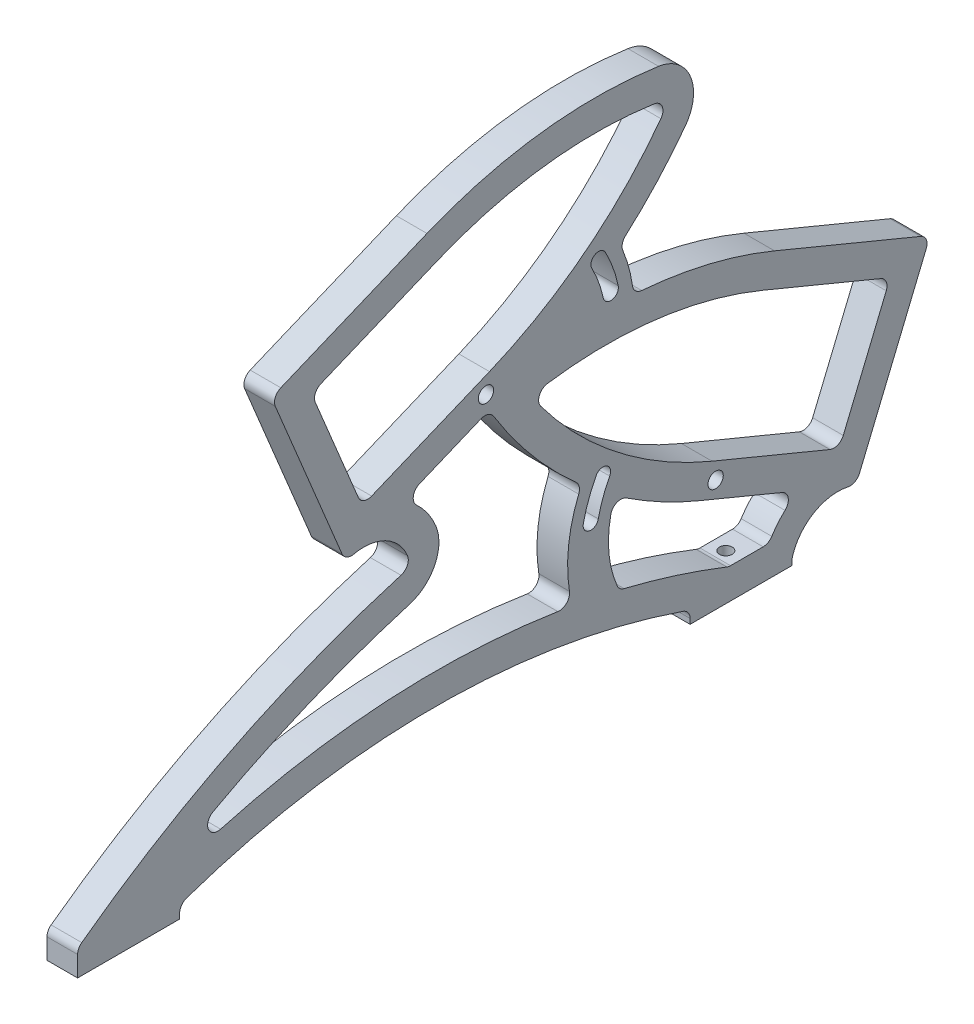
SolidWorks part; units mm, degrees
material "1060 Alloy"
ref_plane "Front Plane" through (0, 0, 0) normal (0, 0, 1) x (1, 0, 0)
ref_plane "Top Plane" through (0, 0, 0) normal (0, 1, 0) x (1, 0, 0)
ref_plane "Right Plane" through (0, 0, 0) normal (1, 0, 0) x (0, 0, -1)
sketch "Sketch1" plane through (0, 0, 0) normal (1, 0, 0) x (0, 0, -1)
  line L0 (0, 0) -> (0, 5)
  line L1 (38.8897, 79.8553) -> (54.5797, 41.9762) construction
  line L2 (38.8897, 79.8553) -> (112.8001, 110.47) construction
  line L3 (54.5797, 41.9762) -> (128.4901, 72.5909) construction
  line L4 (41.8855, 77.849) -> (54.1314, 48.2849) construction
  line L5 (112.8001, 110.47) -> (128.4901, 72.5909) construction
  line L6 (20, 1) -> (20, 0)
  line L7 (0, 0) -> (20, 0)
  line L8 (54.1314, 48.2849) -> (81.8478, 59.7654) construction
  line L9 (69.6019, 89.3295) -> (41.8855, 77.849) construction
  line L10 (80, 59) -> (104.4537, 64.1978) construction
  line L11 (102.0737, 70.7368) -> (80, 59) construction
  line L12 (100.5463, 27.1978) -> (125, 22) construction
  line L13 (125, 22) -> (102.9263, 33.7368) construction
  line L14 (166.1103, 42.8553) -> (150.4203, 4.9762) construction
  line L15 (166.1103, 42.8553) -> (92.1999, 73.47) construction
  line L16 (150.4203, 4.9762) -> (76.5099, 35.5909) construction
  line L17 (92.1999, 73.47) -> (76.5099, 35.5909) construction
  line L18 (150.8686, 11.2849) -> (163.1145, 40.849) construction
  line L19 (163.1145, 40.849) -> (135.3981, 52.3295) construction
  line L20 (123.1522, 22.7654) -> (150.8686, 11.2849) construction
  line L21 (156.9916, 26.0669) -> (84.929, 55.9162) construction
  line L22 (48.0084, 63.0669) -> (120.071, 92.9162) construction
  line L23 (152.4922, 7.3652) -> (167.0342, 42.4726)
  line L24 (167.0342, 42.4726) -> (136.5462, 55.1012)
  line L25 (68.4538, 92.1012) -> (37.9658, 79.4726)
  line L26 (37.9658, 79.4726) -> (52.5078, 44.3652)
  line L27 (63.7245, 49.0113) -> (80.6343, 56.0156)
  line L28 (140, 0) -> (140, 1)
  line L29 (152.4922, 7.3652) -> (143.6238, 11.0386) construction
  line L30 (80.6997, 62.537) -> (55.755, 52.2046)
  line L31 (55.755, 52.2046) -> (45.8052, 76.2254)
  line L32 (45.8052, 76.2254) -> (70.7499, 86.5579)
  line L33 (124.3003, 25.537) -> (149.245, 15.2046)
  line L34 (149.245, 15.2046) -> (159.1948, 39.2254)
  line L35 (159.1948, 39.2254) -> (134.2501, 49.5579)
  line L36 (56.0604, 35.7884) -> (62.7895, 38.5756) construction
  line L37 (52.5078, 44.3652) -> (58.8317, 46.9846) construction
  line L38 (122.0042, 19.9937) -> (141.2755, 12.0113)
  line L39 (135.4645, 6) -> (127.5413, 6)
  line L40 (80, 59) -> (91.6023, 59) construction
  line L41 (125, 22) -> (112.3027, 22) construction
  line L43 (140, 0) -> (120, 0)
  line L56 (120, 1) -> (120, 0)
  line L63 (174.6584, 98) -> (-14.1241, 98) construction
  circle A0 centre (80, 59) radius 1.5
  circle A1 centre (125, 22) radius 1.5
  arc A2 (102.0737, 70.7368) -> (104.4537, 64.1978) centre (80, 59) cw construction
  arc A3 (105.9209, 64.5097) -> (103.3981, 71.441) centre (80, 59) ccw
  arc A4 (102.9865, 63.8859) -> (100.7493, 70.0326) centre (80, 59) ccw
  arc A5 (102.9865, 63.8859) -> (105.9209, 64.5097) centre (104.4537, 64.1978) ccw
  arc A6 (103.3981, 71.441) -> (100.7493, 70.0326) centre (102.0737, 70.7368) ccw
  arc A7 (102.9263, 33.7368) -> (100.5463, 27.1978) centre (125, 22) ccw construction
  arc A8 (101.6019, 34.441) -> (99.0791, 27.5097) centre (125, 22) ccw
  arc A9 (104.2507, 33.0326) -> (102.0135, 26.8859) centre (125, 22) ccw
  arc A10 (104.2507, 33.0326) -> (101.6019, 34.441) centre (102.9263, 33.7368) ccw
  arc A11 (99.0791, 27.5097) -> (102.0135, 26.8859) centre (100.5463, 27.1978) ccw
  arc A12 (81.8478, 59.7654) -> (116.6864, 86.8633) centre (49.9981, 136.6573) ccw construction
  arc A13 (116.6864, 86.8633) -> (113.3977, 94.803) centre (112.68, 89.8548) ccw construction
  arc A14 (113.3977, 94.803) -> (69.6019, 89.3295) centre (101.4516, 12.4375) ccw construction
  arc A15 (135.3981, 52.3295) -> (91.6023, 57.803) centre (103.5484, -24.5625) ccw construction
  arc A16 (91.6023, 57.803) -> (88.3136, 49.8633) centre (92.32, 52.8548) ccw construction
  arc A17 (88.3136, 49.8633) -> (123.1522, 22.7654) centre (155.0019, 99.6573) ccw construction
  arc A18 (106.2569, 71.3115) -> (108.8921, 61.4991) centre (80, 59) cw
  arc A19 (106.2569, 71.3115) -> (119.0902, 85.0685) centre (49.9981, 136.6573) ccw
  arc A20 (119.0902, 85.0685) -> (113.8283, 97.7719) centre (112.68, 89.8548) ccw
  arc A21 (113.8283, 97.7719) -> (68.4538, 92.1012) centre (101.4516, 12.4375) ccw
  arc A23 (80.6343, 56.0156) -> (98.7431, 34.3115) centre (155.0019, 99.6573) ccw
  arc A24 (152.4922, 7.3652) -> (140.0944, 1.6073) centre (148.9396, -1.2116) ccw
  arc A25 (140.0944, 1.6073) -> (140, 1) centre (142, 1) ccw
  arc A26 (20, 1) -> (21.3514, 2.8919) centre (22, 1) cw
  arc A27 (52.5078, 44.3652) -> (64.6372, 39.341) centre (56.0604, 35.7884) cw
  arc A28 (70.7499, 86.5579) -> (112.9671, 91.8341) centre (101.4516, 12.4375) cw
  arc A29 (112.9671, 91.8341) -> (114.2826, 88.6582) centre (112.68, 89.8548) cw
  arc A30 (114.2826, 88.6582) -> (80.6997, 62.537) centre (49.9981, 136.6573) cw
  arc A36 (134.2501, 49.5579) -> (92.0329, 54.8341) centre (103.5484, -24.5625) ccw
  arc A37 (92.0329, 54.8341) -> (90.7174, 51.6582) centre (92.32, 52.8548) ccw
  arc A38 (90.7174, 51.6582) -> (124.3003, 25.537) centre (155.0019, 99.6573) ccw
  arc A44 (120, 1) -> (118.6486, 2.8919) centre (118, 1) ccw
  arc A45 (118.6486, 2.8919) -> (21.3514, 2.8919) centre (70, -139) ccw
  arc A46 (64.6372, 39.341) -> (63.3526, 36.6565) centre (62.7895, 38.5756) cw
  arc A47 (63.3526, 36.6565) -> (0, 5) centre (119.662, -155.253) ccw
  arc A48 (98.7431, 34.3115) -> (96.9455, 14.6553) centre (125, 22) ccw
  arc A49 (96.9455, 14.6553) -> (10.8239, 5.3405) centre (70, -139) ccw
  arc A50 (10.8239, 5.3405) -> (65.0419, 30.8992) centre (119.662, -155.253) cw
  arc A51 (63.7245, 49.0113) -> (70.1805, 41.6371) centre (56.0604, 35.7884) cw
  arc A52 (65.0419, 30.8992) -> (70.1805, 41.6371) centre (62.7895, 38.5756) ccw
  arc A53 (105.2771, 29.2117) -> (106.1445, 12.755) centre (125, 22) ccw
  arc A54 (106.1445, 12.755) -> (127.5413, 6) centre (70, -139) cw
  arc A55 (141.2755, 12.0113) -> (135.4645, 6) centre (148.9396, -1.2116) ccw
  arc A56 (136.5462, 55.1012) -> (108.8921, 61.4991) centre (103.5484, -24.5625) ccw
  arc A57 (122.0042, 19.9937) -> (105.2771, 29.2117) centre (155.0019, 99.6573) cw
  point P17 (103.4923, 67.5505)
  point P22 (101.5077, 30.5505)
  dimension "D1" = 3
  dimension "D3" = 1.5
  dimension "D8" = 5
  dimension "D11" = 22
  dimension "D12" = 80
  dimension "D14" = 22.5
  dimension "D16" = 2
  dimension "D17" = 6
  dimension "D21" = 30
  dimension "D22" = 35
  dimension "D23" = 80
  dimension "D24" = 3
  dimension "D18" = 6
  dimension "D29" = 59
  dimension "D25" = 5
  dimension "D28" = 2
  dimension "D36" = 3
  dimension "D37" = 3
  dimension "D38" = 3
  dimension "D39" = 8
  dimension "D40" = 12
  dimension "D45" = 3
  dimension "D46" = 3
  dimension "D47" = 16
  dimension "D48" = 12
  dimension "D49" = 3
  dimension "D52" = 3
  dimension "D53" = 16
  dimension "D54" = 4
  dimension "D56" = 2
  dimension "D57" = 150
  dimension "D58" = 2
  dimension "D59" = 200
  dimension "D60" = 6
  dimension "D61" = 6
  dimension "D62" = 4
  dimension "D63" = 6
  dimension "D64" = 8
  dimension "D67" = 4
  dimension "D68" = 6
  dimension "D69" = 6
  dimension "D2" = 25
  dimension "D4" = 25
  dimension "D7" = 125
  dimension "D9" = 20
  dimension "D10" = 100
  dimension "D13" = 1
  dimension "D15" = 22.5
  dimension "D19" = 30
  dimension "D20" = 30
  dimension "D26" = 3
  dimension "D27" = 2
  dimension "D30" = 3
  dimension "D31" = 3
  dimension "D32" = 98
  dimension "D33" = 3
  dimension "D34" = 3
  dimension "D35" = 3
  dimension "D41" = 3
  dimension "D42" = 3
  dimension "D43" = 3
  dimension "D44" = 3
  dimension "D50" = 3
  dimension "D51" = 3
  dimension "D65" = 6
  dimension "D66" = 3
extrude "Boss-Extrude1" add sketch "Sketch1" along normal blind 6
fillet "Fillet1" radius 2 21 edges at (3, 14.6553, -96.9455) (3, 34.3115, -98.7431) (3, 12.755, -106.1445) (3, 12.0113, -141.2755) (3, 6, -135.4645) (3, 6, -127.5413) (3, 15.2046, -149.245) (3, 39.2254, -159.1948) (3, 42.4726, -167.0342) (3, 7.3652, -152.4922) (3, 52.2046, -55.755) (3, 79.4726, -37.9658) (3, 76.2254, -45.8052) (3, 44.3652, -52.5078) (3, 49.0113, -63.7245) (3, 5.3405, -10.8239) (3, 5, 0) (3, 61.4991, -108.8921) (3, 71.3115, -106.2569) (3, 29.2117, -105.2771) (3, 56.0156, -80.6343)
hole_wizard "Tap Drill for M3 Tap1" positions "Sketch3" profile "Sketch2" hole size "M3" standard "ISO"
sketch "Sketch3" plane through (0, 0, 0) normal (0, -1, 0) x (-1, 0, 0)
  line L0 (-6, 20) -> (0, 20) construction
  line L1 (0, 0) -> (0, 20) construction
  line L2 (-6, 120) -> (0, 120) construction
  point P0 (-3, 10)
  point P2 (-3, 130)
  dimension "D1" = 10
  dimension "D2" = 3
  dimension "D3" = 10
sketch "Sketch2" plane through (3, 0, -10) normal (1, 0, 0) x (0, 0, -1)
  line L0 (0, 0) -> (0, 10.7511)
  line L1 (0, 10.7511) -> (1.25, 10)
  line L2 (1.25, 10) -> (1.25, 0)
  line L5 (1.25, 0) -> (0, 0)
  line L10 (0, 10.7511) -> (-1.25, 10) construction
  line L11 (0, -6.35) -> (0, 107.95) construction
  dimension "Hole Dia." = 2.5
  dimension "Hole Depth" = 10
  dimension "Drill Angle" = 118
equation "\"ˇ35\"=76.24"
